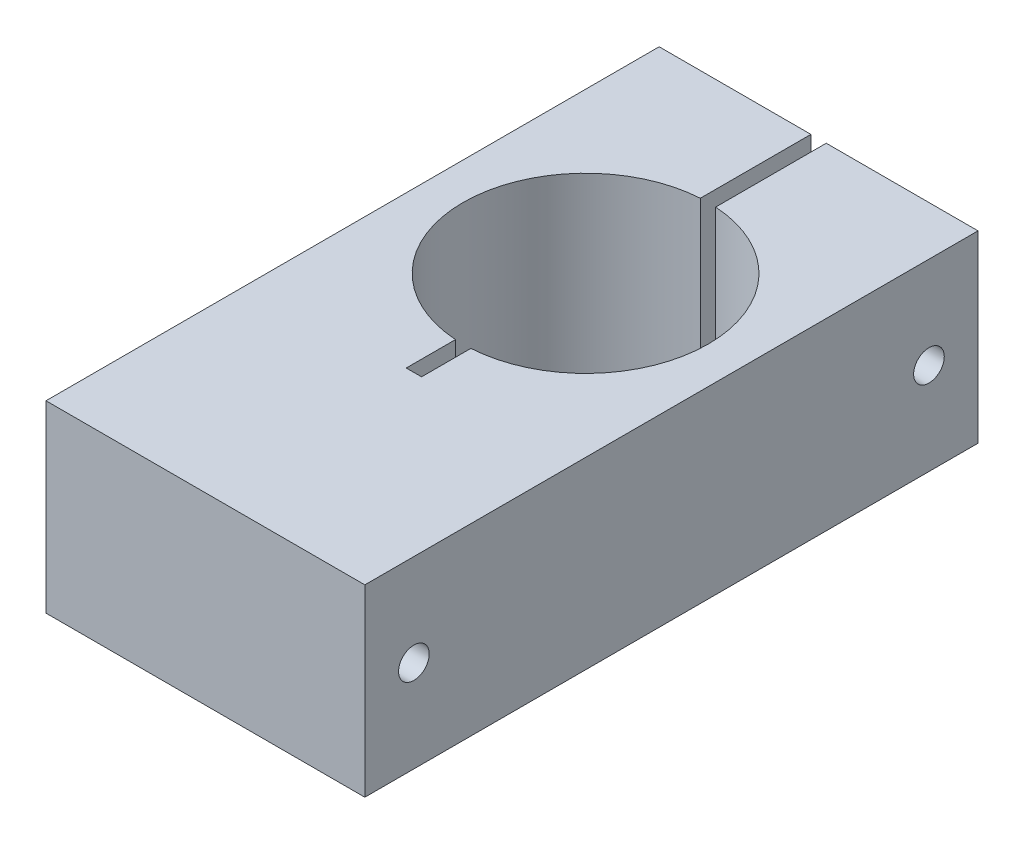
SolidWorks part; units mm, degrees
ref_plane "Front" through (0, 0, 0) normal (0, 0, 1) x (1, 0, 0)
ref_plane "Top" through (0, 0, 0) normal (0, 1, 0) x (1, 0, 0)
ref_plane "Right" through (0, 0, 0) normal (1, 0, 0) x (0, 0, -1)
sketch "Sketch1" plane through (0, 0, 0) normal (0, 1, 0) x (1, 0, 0)
  line L1 (-16.51, 31.75) -> (16.51, 31.75)
  line L2 (-16.51, 31.75) -> (-16.51, -31.75)
  line L3 (-16.51, -31.75) -> (16.51, -31.75)
  line L4 (16.51, 31.75) -> (16.51, -31.75)
  line L5 (-16.51, 31.75) -> (16.51, -31.75) construction
  line L6 (-16.51, -31.75) -> (16.51, 31.75) construction
  point P0 (0, 0)
extrude "Boss-Extrude1" add sketch "Sketch1" along normal blind 19.05
sketch "Sketch2" plane through (0, 19.05, 0) normal (0, 1, 0) x (1, 0, 0)
  line L1 (16.51, 31.75) -> (-16.51, 31.75) construction
  line L3 (0, 31.75) -> (0.7938, 31.75)
  line L5 (0, 31.75) -> (-0.7937, 31.75)
  line L6 (-0.7937, 31.75) -> (-0.7937, -10.16)
  line L8 (0.7938, 31.75) -> (0.7938, -10.16)
  line L9 (-0.7937, -10.16) -> (0.7938, -10.16)
extrude "Cut-Extrude1" cut sketch "Sketch2" against normal blind 19.05
sketch "Sketch3" plane through (0, 19.05, 0) normal (0, 1, 0) x (1, 0, 0)
  circle A0 centre (0, 7.62) radius 12.7
extrude "Cut-Extrude2" cut sketch "Sketch3" against normal blind 19.05
sketch "Sketch4" plane through (16.51, 0, 0) normal (1, 0, 0) x (0, 0, -1)
  circle A0 centre (-26.67, 9.525) radius 1.5875
  circle A1 centre (26.67, 9.525) radius 1.5875
extrude "Cut-Extrude3" cut sketch "Sketch4" against normal up to surface (33.02 mm away) up to face at (-16.51, 9.525, 0)
